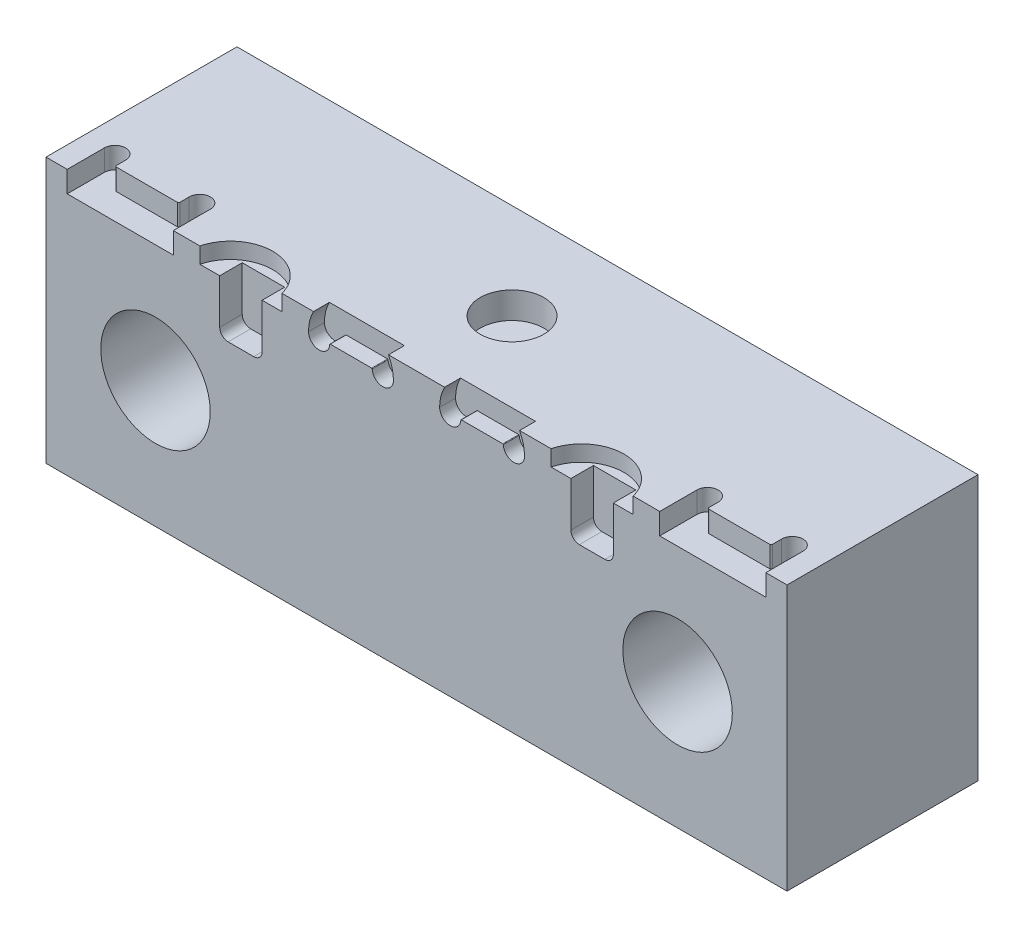
SolidWorks part; units mm, degrees
ref_plane "Front Plane" through (0, 0, 0) normal (0, 0, 1) x (1, 0, 0)
ref_plane "Top Plane" through (0, 0, 0) normal (0, 1, 0) x (1, 0, 0)
ref_plane "Right Plane" through (0, 0, 0) normal (1, 0, 0) x (0, 0, -1)
sketch "Sketch1" plane through (0, 0, 0) normal (1, 0, 0) x (0, 0, -1)
  line L1 (-18, -25) -> (18, -25)
  line L2 (-18, -25) -> (-18, 25)
  line L3 (-18, 25) -> (18, 25)
  line L4 (18, -25) -> (18, 25)
  line L5 (-18, -25) -> (18, 25) construction
  line L6 (-18, 25) -> (18, -25) construction
  point P0 (0, 0)
  dimension "D1" = 36
  dimension "D2" = 50
extrude "Boss-Extrude1" add sketch "Sketch1" along normal mid plane 139.7
hole_wizard "CBORE for 1/2 Socket Head Cap Screw1" positions "Sketch2" profile "Sketch3" counterbore size "1/2" standard "ANSI Inch" end condition through all
sketch "Sketch2" plane through (0, 0, 18) normal (0, 0, 1) x (1, 0, 0)
  line L0 (69.85, -25) -> (-69.85, -25) construction
  point P0 (-49.2125, -1.124)
  point P2 (49.2125, -1.124)
  dimension "D1" = 23.876
  dimension "D2" = 98.425
  dimension "D3" = 49.2125
sketch "Sketch3" plane through (-49.2125, -1.124, 18) normal (1, 0, 0) x (0, -1, 0)
  line L0 (0, 0) -> (0, 36)
  line L1 (0, 36) -> (6.9456, 36)
  line L3 (6.9456, 36) -> (6.9456, 27.94)
  line L4 (6.9456, 27.94) -> (10.3187, 27.94)
  line L5 (10.3187, 27.94) -> (10.3187, 0)
  line L7 (10.3187, 0) -> (0, 0)
  line L11 (0, -6.35) -> (0, 107.95) construction
  dimension "Thru Hole Dia." = 13.8913
  dimension "Thru Hole Depth" = 36
  dimension "C'Bore Dia." = 20.6375
  dimension "C'Bore Depth" = 27.94
sketch "Sketch4" plane through (0, -25, 0) normal (0, -1, 0) x (-1, 0, 0)
  text T0 "BOTTOM"
sketch "Sketch5" plane through (0, 25, 0) normal (0, 1, 0) x (1, 0, 0)
  line L0 (69.85, -18) -> (-69.85, -18) construction
  line L1 (-65.85, -18) -> (-45.85, -18)
  line L2 (-65.85, -18) -> (-65.85, -11)
  line L3 (69.85, 18) -> (69.85, -18) construction
  line L5 (-69.85, 18) -> (-69.85, -18) construction
  line L6 (45.85, -18) -> (65.85, -18)
  line L7 (45.85, -18) -> (45.85, -11)
  line L8 (-61.85, -11) -> (-61.85, -13)
  line L9 (65.85, -18) -> (65.85, -11)
  line L10 (-61.85, -13) -> (-49.85, -13)
  line L11 (-49.85, -13) -> (-49.85, -11)
  line L12 (-45.85, -11) -> (-45.85, -18)
  line L14 (49.85, -11) -> (49.85, -13)
  line L15 (49.85, -13) -> (61.85, -13)
  line L16 (61.85, -13) -> (61.85, -11)
  arc A0 (-65.85, -11) -> (-61.85, -11) centre (-63.85, -11) cw
  arc A1 (-49.85, -11) -> (-45.85, -11) centre (-47.85, -11) cw
  arc A2 (45.85, -11) -> (49.85, -11) centre (47.85, -11) cw
  arc A3 (61.85, -11) -> (65.85, -11) centre (63.85, -11) cw
  dimension "D6" = 2
  dimension "D7" = 2
  dimension "D8" = 2
  dimension "D9" = 2
  dimension "D1" = 20
  dimension "D2" = 20
  dimension "D3" = 4
  dimension "D4" = 4
  dimension "D5" = 5
  dimension "D10" = 2
extrude "Cut-Extrude1" cut sketch "Sketch5" against normal blind 4
sketch "Sketch6" plane through (0, 25, 0) normal (0, 1, 0) x (1, 0, 0)
  line L0 (69.85, -18) -> (65.85, -18) construction
  line L2 (-40.85, -18) -> (-25.3581, -18)
  line L3 (25.3581, -18) -> (40.85, -18)
  line L4 (-45.85, -18) -> (-45.85, -11) construction
  line L5 (45.85, -11) -> (45.85, -18) construction
  arc A0 (-40.85, -18) -> (-25.3581, -18) centre (-33.104, -20) cw
  arc A1 (25.3581, -18) -> (40.85, -18) centre (33.104, -20) cw
  dimension "D1" = 8
  dimension "D2" = 2
  dimension "D3" = 5
  dimension "D5" = 5
  dimension "D4" = 2
extrude "Cut-Extrude2" cut sketch "Sketch6" against normal blind 3
sketch "Sketch8" plane through (0, 0, 18) normal (0, 0, 1) x (1, 0, 0)
  line L0 (-37.104, 22) -> (-29.104, 22)
  line L1 (-25.3581, 22) -> (-40.85, 22) construction
  line L2 (-40.85, 22) -> (-25.3581, 22) construction
  line L3 (-29.104, 22) -> (-29.104, 13.5875)
  line L4 (-30.6915, 12) -> (-35.5165, 12)
  line L5 (-37.104, 13.5875) -> (-37.104, 22)
  line L6 (29.104, 22) -> (37.104, 22)
  line L7 (35.5165, 12) -> (30.6915, 12)
  line L8 (37.104, 22) -> (37.104, 13.5875)
  line L9 (29.104, 13.5875) -> (29.104, 22)
  line L10 (25.3581, 22) -> (40.85, 22) construction
  arc A0 (-29.104, 13.5875) -> (-30.6915, 12) centre (-30.6915, 13.5875) cw
  arc A1 (-35.5165, 12) -> (-37.104, 13.5875) centre (-35.5165, 13.5875) cw
  arc A2 (37.104, 13.5875) -> (35.5165, 12) centre (35.5165, 13.5875) cw
  arc A3 (30.6915, 12) -> (29.104, 13.5875) centre (30.6915, 13.5875) cw
  point P7 (-33.104, 22)
  point P11 (-29.104, 12)
  point P14 (-37.104, 12)
  point P15 (33.104, 22)
  dimension "D3" = 1.5875
  dimension "D1" = 8
  dimension "D2" = 10
  dimension "D4" = 2
extrude "Cut-Extrude4" cut sketch "Sketch8" against normal blind 4.25
sketch "Sketch9" plane through (0, 0, 18) normal (0, 0, 1) x (1, 0, 0)
  line L0 (69.85, 25) -> (65.85, 25) construction
  line L1 (-16.3581, 21.25) -> (-8.3581, 21.25)
  line L3 (-19.4247, 25) -> (-5.2914, 25)
  line L4 (5.2914, 25) -> (19.4247, 25)
  line L5 (8.3581, 21.25) -> (16.3581, 21.25)
  line L7 (-25.3581, 22) -> (-25.3581, 25) construction
  line L9 (25.3581, 22) -> (25.3581, 25) construction
  arc A0 (-20.3581, 21.25) -> (-19.4247, 25) centre (-12.3581, 21.25) cw
  arc A1 (-5.2914, 25) -> (-4.3581, 21.25) centre (-12.3581, 21.25) cw
  arc A2 (-20.3581, 21.25) -> (-16.3581, 21.25) centre (-18.3581, 21.25) ccw
  arc A3 (-8.3581, 21.25) -> (-4.3581, 21.25) centre (-6.3581, 21.25) ccw
  arc A4 (16.3581, 21.25) -> (20.3581, 21.25) centre (18.3581, 21.25) ccw
  arc A5 (4.3581, 21.25) -> (8.3581, 21.25) centre (6.3581, 21.25) ccw
  arc A6 (4.3581, 21.25) -> (5.2914, 25) centre (12.3581, 21.25) cw
  arc A7 (19.4247, 25) -> (20.3581, 21.25) centre (12.3581, 21.25) cw
  dimension "D1" = 8
  dimension "D3" = 2
  dimension "D4" = 2
  dimension "D2" = 3.75
  dimension "D5" = 5
  dimension "D7" = 5
  dimension "D6" = 2
extrude "Cut-Extrude5" cut sketch "Sketch9" against normal blind 3
sketch "Sketch10" plane through (0, 25, 0) normal (0, 1, 0) x (1, 0, 0)
  circle A0 centre (0, 0) radius 6
  dimension "D1" = 12
extrude "Cut-Extrude6" cut sketch "Sketch10" against normal blind 5
fillet "Fillet1" radius 0.1 4 edges at (16.3581, 21.25, 16.5) (8.3581, 21.25, 16.5) (-8.3581, 21.25, 16.5) (-16.3581, 21.25, 16.5)
ref_point "Point1"
sketch "Sketch11" plane through (0, 25, 0) normal (0, 1, 0) x (1, 0, 0)
  circle A0 centre (0, 0) radius 6 construction
  point P0 (0, 0)
fillet "Fillet2" radius 0.254 4 edges at (61.85, 23, 13) (49.85, 23, 13) (-61.85, 23, 13) (-49.85, 23, 13)
